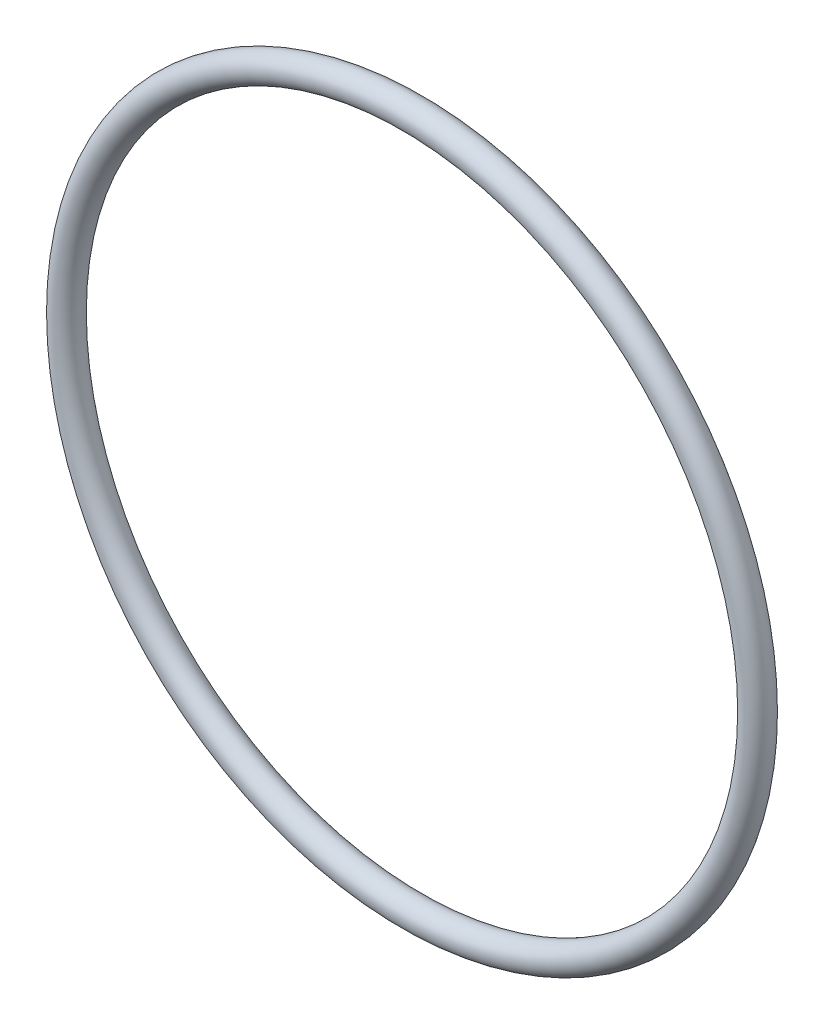
SolidWorks part; units mm, degrees
material "High Temp Silicon"
ref_plane "Front" through (0, 0, 0) normal (0, 0, 1) x (1, 0, 0)
ref_plane "Top" through (0, 0, 0) normal (0, 1, 0) x (1, 0, 0)
ref_plane "Right" through (0, 0, 0) normal (1, 0, 0) x (0, 0, -1)
sketch "Sketch1" plane through (0, 0, 0) normal (1, 0, 0) x (0, -1, 0)
  line L0 (0, -1.3081) -> (0, 1.3081) construction
  line L2 (-36.7551, 0) -> (36.7551, 0) construction
  line L3 (-30.7975, 0) -> (30.7975, 0) construction
  circle A0 centre (32.1056, 0) radius 1.3081
  point P9 (30.7975, 0)
  point P10 (33.4137, 0)
  point P13 (32.1056, 1.3081)
  point P14 (32.1056, -1.3081)
  dimension "Width" = 2.6162
  dimension "ID" = 61.595
revolve "Revolve1" add sketch "Sketch1" angle 360 about L0
